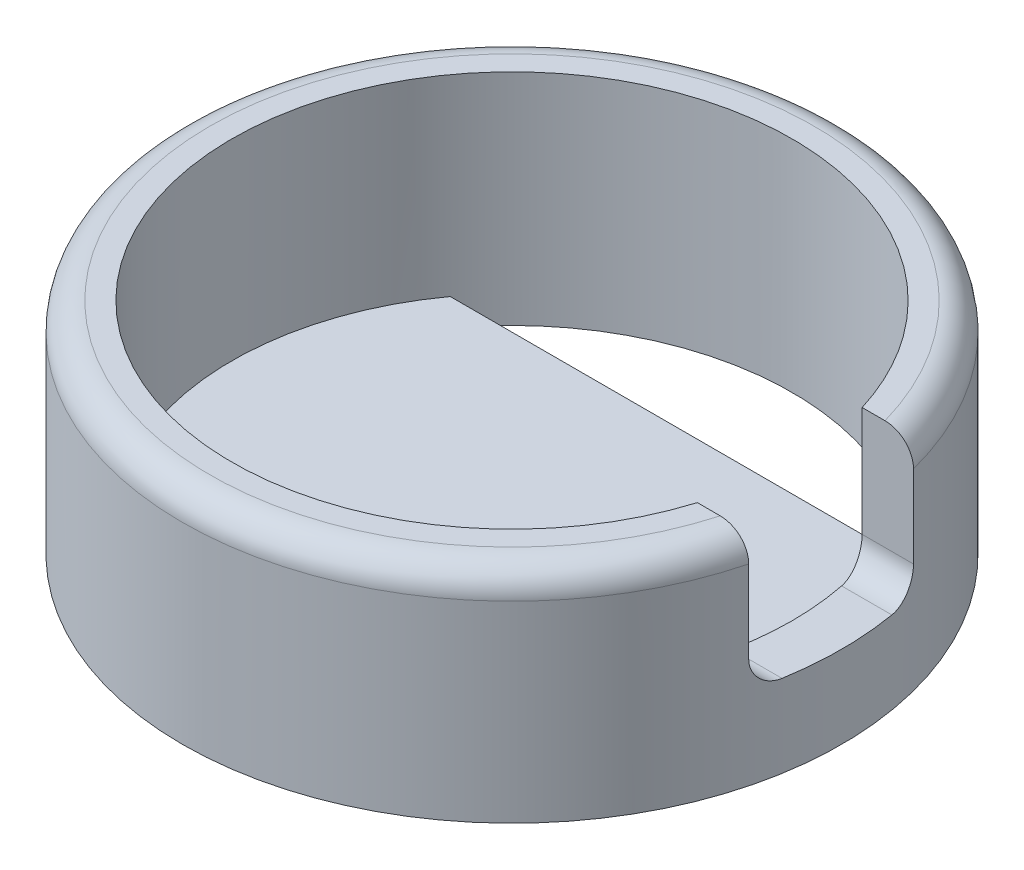
SolidWorks part; units mm, degrees
ref_plane "Front Plane" through (0, 0, 0) normal (0, 0, 1) x (1, 0, 0)
ref_plane "Top Plane" through (0, 0, 0) normal (0, 1, 0) x (1, 0, 0)
ref_plane "Right Plane" through (0, 0, 0) normal (1, 0, 0) x (0, 0, -1)
sketch "Sketch1" plane through (0, 0, 0) normal (0, 1, 0) x (1, 0, 0)
  circle A0 centre (0, 0) radius 6
  circle A1 centre (0, 0) radius 5.1
  dimension "D1" = 12
  dimension "D2" = 10.2
extrude "Boss-Extrude1" add sketch "Sketch1" along normal blind 3.5
sketch "Sketch4" plane through (0, 0, 0) normal (0, -1, 0) x (1, 0, 0)
  circle A0 centre (0, 0) radius 6 construction
  circle A1 centre (0, 0) radius 6
extrude "Boss-Extrude2" add sketch "Sketch4" along normal blind 0.5
sketch "Sketch5" plane through (0, 3.5, 0) normal (0, -1, 0) x (1, 0, 0)
  line L1 (0, 1.5) -> (6, 1.5)
  line L2 (0, 1.5) -> (0, -1.5)
  line L3 (0, -1.5) -> (6, -1.5)
  line L4 (6, 1.5) -> (6, -1.5)
  circle A0 centre (0, 0) radius 6 construction
  dimension "D1" = 3
extrude "Cut-Extrude3" cut sketch "Sketch5" along normal blind 2.5
sketch "Sketch7" plane through (0, 0, 0) normal (0, 1, 0) x (1, 0, 0)
  line L0 (4.1243, -3) -> (-4.1243, -3)
  line L1 (4.1243, 3) -> (-4.1243, 3)
  circle A0 centre (0, 0) radius 5.1 construction
  arc A1 (4.8744, 1.5) -> (4.8744, -1.5) centre (0, 0) ccw construction
  arc A2 (4.1243, 3) -> (-4.1243, 3) centre (0, 0) ccw
  arc A3 (-4.1243, -3) -> (4.1243, -3) centre (0, 0) ccw
  dimension "D1" = 6
extrude "Cut-Extrude4" cut sketch "Sketch7" against normal through all
fillet "Fillet1" radius 0.5 3 edges at (5.3419, 1, 1.5) (5.3419, 1, -1.5) (-6, 3.5, 0)
